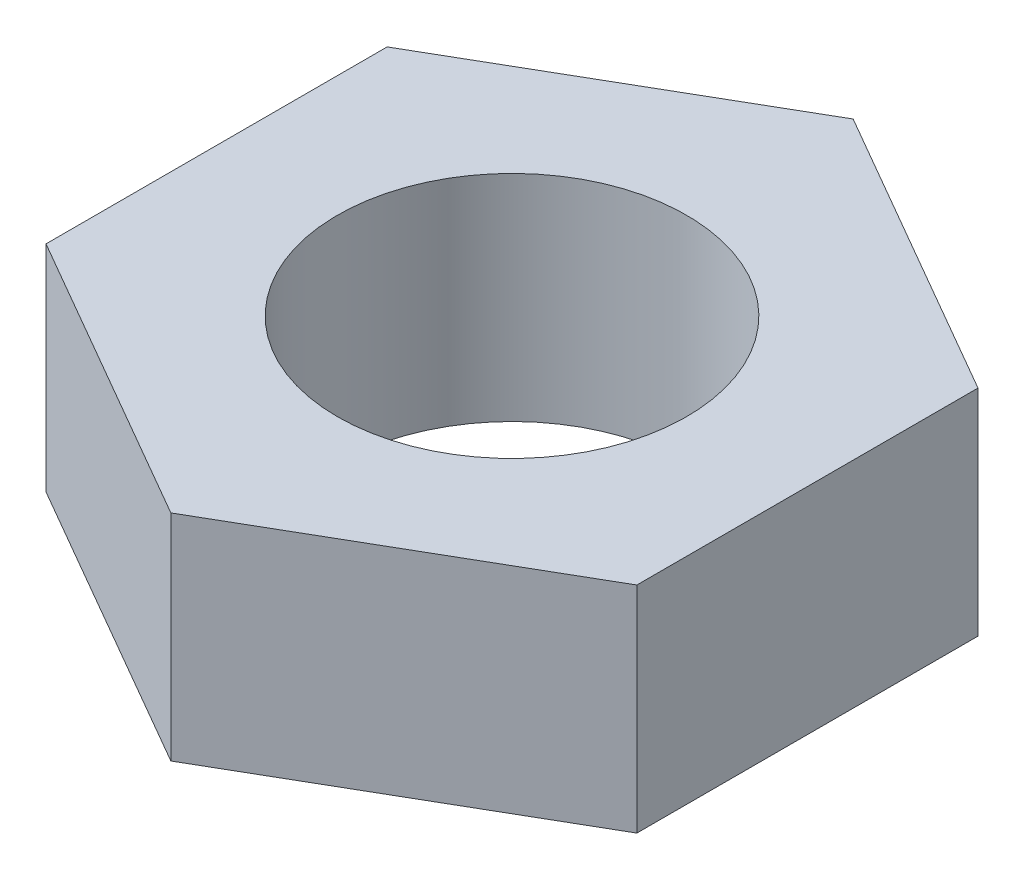
SolidWorks part; units mm, degrees
ref_plane "Ebene vorne" through (0, 0, 0) normal (0, 0, 1) x (1, 0, 0)
ref_plane "Ebene oben" through (0, 0, 0) normal (0, 1, 0) x (1, 0, 0)
ref_plane "Ebene rechts" through (0, 0, 0) normal (1, 0, 0) x (0, 0, -1)
sketch "Skizze1" plane through (0, 0, 0) normal (0, 1, 0) x (1, 0, 0)
  line L1 (5.5, 3.1754) -> (0, 6.3509)
  line L2 (0, 6.3509) -> (-5.5, 3.1754)
  line L3 (-5.5, 3.1754) -> (-5.5, -3.1754)
  line L4 (-5.5, -3.1754) -> (0, -6.3509)
  line L5 (0, -6.3509) -> (5.5, -3.1754)
  line L6 (5.5, -3.1754) -> (5.5, 3.1754)
  circle A0 centre (0, 0) radius 5.5 construction
  circle A1 centre (0, 0) radius 3.25
  dimension "D2" = 6.5
  dimension "D1" = 11
extrude "Aufsatz-Linear austragen1" add sketch "Skizze1" along normal blind 4
